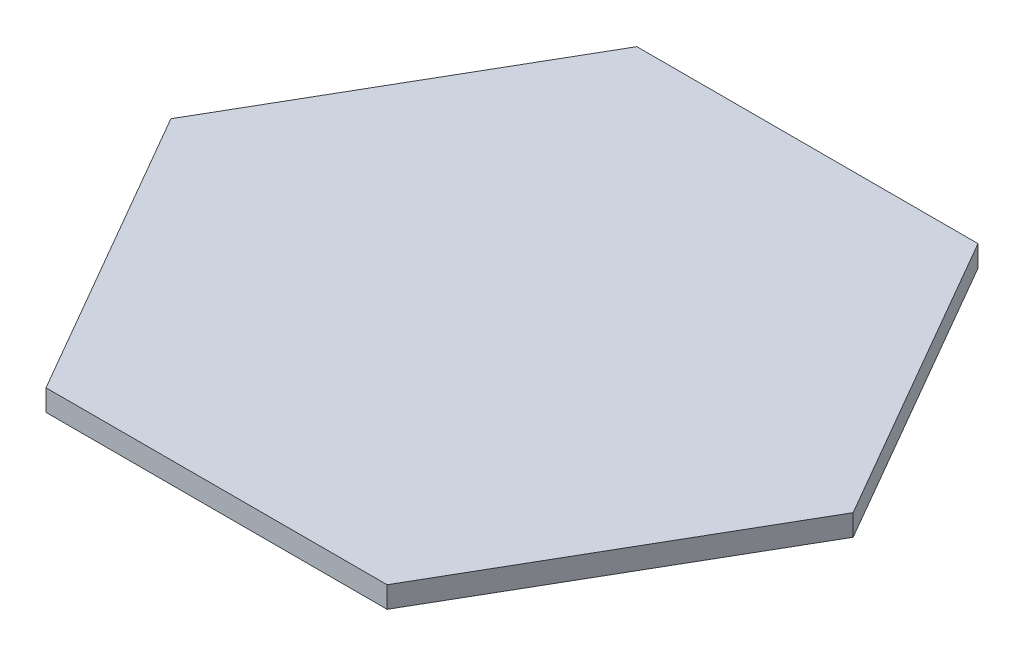
SolidWorks part; units mm, degrees
material "Cedar"
ref_plane "Front Plane" through (0, 0, 0) normal (0, 0, 1) x (1, 0, 0)
ref_plane "Top Plane" through (0, 0, 0) normal (0, 1, 0) x (1, 0, 0)
ref_plane "Right Plane" through (0, 0, 0) normal (1, 0, 0) x (0, 0, -1)
sketch "Sketch1" plane through (0, 0, 0) normal (0, 1, 0) x (1, 0, 0)
  line L0 (0, 0) -> (50.8, 0) construction
  line L1 (50.8, 0) -> (25.4, 43.9941)
  line L2 (25.4, 43.9941) -> (-25.4, 43.9941)
  line L3 (-25.4, 43.9941) -> (-50.8, 0)
  line L4 (-50.8, 0) -> (-25.4, -43.9941)
  line L5 (-25.4, -43.9941) -> (25.4, -43.9941)
  line L6 (25.4, -43.9941) -> (50.8, 0)
  circle A0 centre (0, 0) radius 43.9941 construction
  dimension "D1" = 50.8
extrude "Boss-Extrude1" add sketch "Sketch1" along normal blind 3.175
